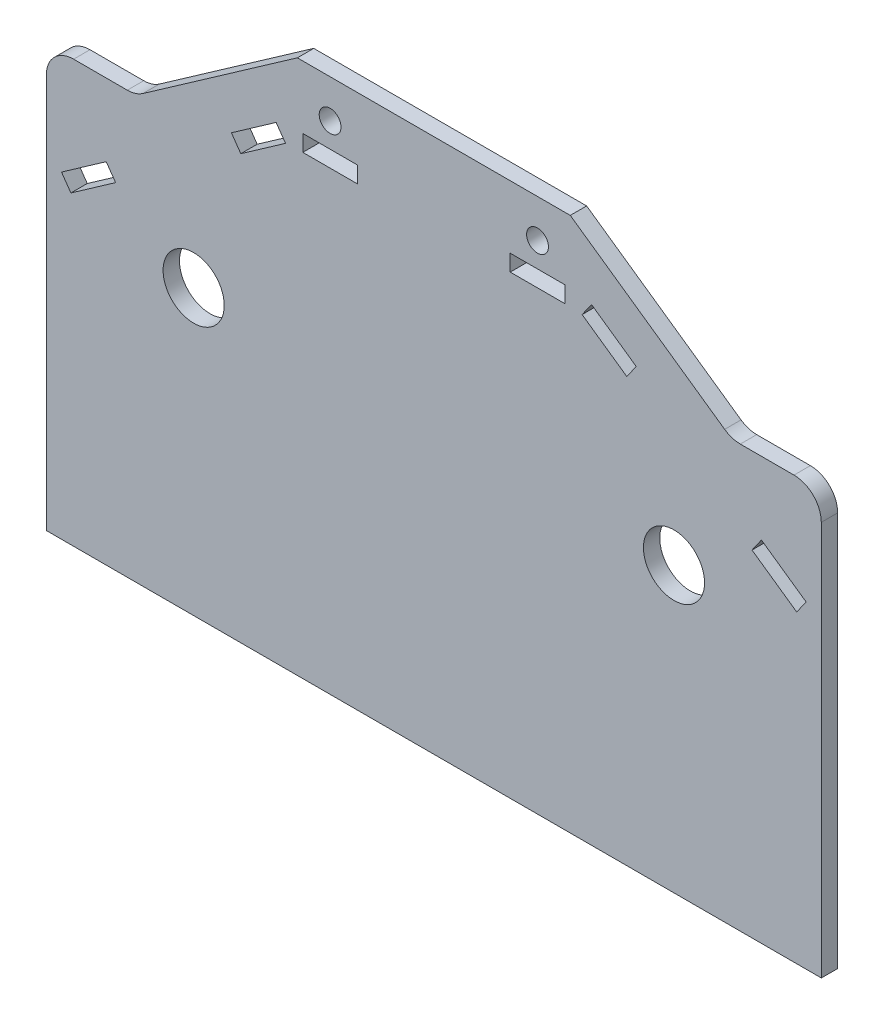
SolidWorks part; units mm, degrees
ref_plane "Alzado" through (0, 0, 0) normal (0, 0, 1) x (1, 0, 0)
ref_plane "Planta" through (0, 0, 0) normal (0, 1, 0) x (1, 0, 0)
ref_plane "Vista lateral" through (0, 0, 0) normal (1, 0, 0) x (0, 0, -1)
sketch "Model" plane through (0, 0, 0) normal (0, 0, 1) x (1, 0, 0)
  line L0 (40.6568, 68.2) -> (-1.7, 68.2)
  line L1 (48.3, 68.2) -> (40.6568, 68.2)
  line L2 (94.3, -29.8) -> (94.2898, 42.4913)
  line L3 (73.3, -29.8) -> (94.3, -29.8)
  line L4 (-18.9469, -29.8) -> (62.3, -29.8)
  line L5 (-47.7, -29.8) -> (-18.9469, -29.8)
  line L6 (-47.6898, 42.4913) -> (-47.7, -29.8)
  line L7 (9.3, 53.7) -> (9.3, 56.7)
  line L8 (9.3, 56.7) -> (-0.7, 56.7)
  line L9 (-0.7, 56.7) -> (-0.7, 53.7)
  line L10 (-0.7, 53.7) -> (9.3, 53.7)
  line L11 (58.6608, 47.8096) -> (60.3816, 50.2671)
  line L12 (60.3816, 50.2671) -> (52.1901, 56.0029)
  line L13 (52.1901, 56.0029) -> (50.4693, 53.5454)
  line L14 (50.4693, 53.5454) -> (58.6608, 47.8096)
  line L15 (37.3, 53.7) -> (37.3, 56.7)
  line L16 (37.3, 56.7) -> (47.3, 56.7)
  line L17 (47.3, 56.7) -> (47.3, 53.7)
  line L18 (47.3, 53.7) -> (37.3, 53.7)
  line L19 (-12.0608, 47.8096) -> (-13.7816, 50.2671)
  line L20 (-13.7816, 50.2671) -> (-5.5901, 56.0029)
  line L21 (-5.5901, 56.0029) -> (-3.8693, 53.5454)
  line L22 (-3.8693, 53.5454) -> (-12.0608, 47.8096)
  line L23 (-34.9971, 31.7495) -> (-36.7178, 34.2069)
  line L24 (-36.7178, 34.2069) -> (-44.9094, 28.4712)
  line L25 (-44.9094, 28.4712) -> (-43.1886, 26.0137)
  line L26 (-43.1886, 26.0137) -> (-34.9971, 31.7495)
  line L27 (81.5971, 31.7495) -> (83.3178, 34.2069)
  line L28 (83.3178, 34.2069) -> (91.5094, 28.4712)
  line L29 (91.5094, 28.4712) -> (89.7886, 26.0137)
  line L30 (89.7886, 26.0137) -> (81.5971, 31.7495)
  line L31 (48.3, 68.2) -> (76.5847, 48.3948)
  line L32 (-1.7, 68.2) -> (-29.9847, 48.3948)
  line L33 (89.2898, 47.4906) -> (79.4526, 47.4906)
  line L34 (-42.6898, 47.4906) -> (-32.8526, 47.4906)
  line L35 (69.8366, -29.8) -> (73.3, -29.8)
  line L36 (62.3, -29.8) -> (69.8366, -29.8)
  circle A0 centre (-20.7, 22.2) radius 5.6027
  circle A1 centre (67.3, 22.2) radius 5.6027
  circle A2 centre (42.3, 61.2) radius 2
  circle A3 centre (4.3, 61.2) radius 2
  arc A4 (76.5847, 48.3948) -> (79.4526, 47.4906) centre (79.4526, 52.4906) ccw
  arc A5 (-32.8526, 47.4906) -> (-29.9847, 48.3948) centre (-32.8526, 52.4906) ccw
  arc A6 (94.2898, 42.4913) -> (89.2898, 47.4906) centre (89.2898, 42.4906) ccw
  arc A7 (-42.6898, 47.4906) -> (-47.6898, 42.4913) centre (-42.6898, 42.4906) ccw
extrude "Saliente-Extruir1" add sketch "Model" along normal blind 3
